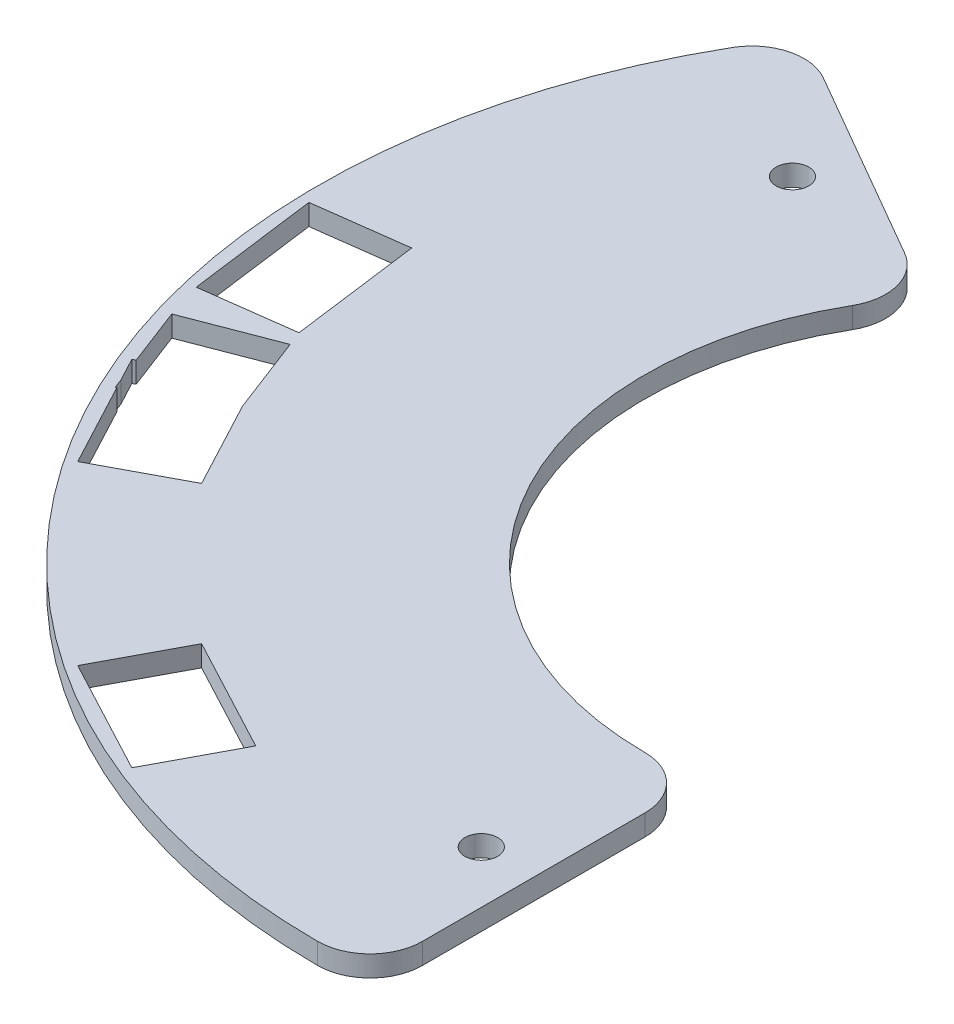
SolidWorks part; units mm, degrees
ref_plane "Front Plane" through (0, 0, 0) normal (0, 0, 1) x (1, 0, 0)
ref_plane "Top Plane" through (0, 0, 0) normal (0, 1, 0) x (1, 0, 0)
ref_plane "Right Plane" through (0, 0, 0) normal (1, 0, 0) x (0, 0, -1)
sketch "Sketch3" plane through (0, 0, 0) normal (0, 1, 0) x (1, 0, 0)
  line L0 (0, -25) -> (0, -50) construction
  line L1 (-21.6506, 12.5) -> (-43.3013, 25) construction
  line L2 (-41.1625, 28.384) -> (-19.3717, 15.8031)
  line L3 (4, -24.6779) -> (4, -49.8397)
  arc A0 (-19.3717, 15.8031) -> (4, -24.6779) centre (0, 0) ccw
  arc A1 (-41.1625, 28.384) -> (4, -49.8397) centre (0, 0) ccw
  circle A2 centre (0, 0) radius 37.5 construction
  circle A3 centre (-32.476, 18.75) radius 1.25
  circle A4 centre (0, -37.5) radius 1.25
  dimension "D1" = 100
  dimension "D2" = 50
  dimension "D6" = 75
  dimension "D7" = 2.5
  dimension "D3" = 120
  dimension "D4" = 4
  dimension "D5" = 4
extrude "Boss-Extrude2" add sketch "Sketch3" along normal mid plane 1.6
sketch "Sketch4" plane through (0, 0, 0) normal (0, 1, 0) x (1, 0, 0)
  line L0 (0, 0) -> (0, -45.5) construction
  line L1 (0, 0) -> (-21.361, -40.1741) construction
  line L2 (0, 0) -> (-40.1741, -21.361) construction
  line L3 (0, 0) -> (-42.4779, -16.3057) construction
  line L4 (0, 0) -> (-45.1107, -5.9389) construction
  line L5 (-24.1325, -34.7364) -> (-15.3031, -39.4312)
  line L6 (-24.1325, -34.7364) -> (-27.4188, -40.9171)
  line L7 (-15.3031, -39.4312) -> (-18.5894, -45.6118)
  line L8 (-27.4188, -40.9171) -> (-18.5894, -45.6118)
  line L9 (-16.9462, -42.5215) -> (-25.7757, -37.8268) construction
  line L10 (-19.7178, -37.0838) -> (-23.0041, -43.2644) construction
  line L11 (-39.4312, -15.3031) -> (-34.7364, -24.1325)
  line L12 (-39.4312, -15.3031) -> (-45.6118, -18.5894)
  line L13 (-34.7364, -24.1325) -> (-40.9171, -27.4188)
  line L14 (-45.6118, -18.5894) -> (-40.9171, -27.4188)
  line L15 (-37.8268, -25.7757) -> (-42.5215, -16.9462) construction
  line L16 (-37.0838, -19.7178) -> (-43.2644, -23.0041) construction
  line L17 (-40.5543, -11.5505) -> (-37.8665, -18.5524)
  line L18 (-40.5543, -11.5505) -> (-47.0893, -14.0591)
  line L19 (-37.8665, -18.5524) -> (-44.4016, -21.061)
  line L20 (-47.0893, -14.0591) -> (-44.4016, -21.061)
  line L21 (-41.134, -19.8067) -> (-43.8218, -12.8048) construction
  line L22 (-39.2104, -15.0515) -> (-45.7454, -17.56) construction
  line L23 (-42.2933, -0.5249) -> (-40.9881, -10.4393)
  line L24 (-42.2933, -0.5249) -> (-49.2334, -1.4386)
  line L25 (-40.9881, -10.4393) -> (-47.9282, -11.353)
  line L26 (-49.2334, -1.4386) -> (-47.9282, -11.353)
  line L27 (-44.4581, -10.8962) -> (-45.7634, -0.9817) construction
  line L28 (-41.6407, -5.4821) -> (-48.5808, -6.3958) construction
  circle A0 centre (0, 0) radius 45.5 construction
  dimension "D5" = 91
  dimension "D1" = 28
  dimension "D2" = 62
  dimension "D3" = 69
  dimension "D4" = 82.5
  dimension "D6" = 10
  dimension "D7" = 7
  dimension "D8" = 7.5
extrude "Cut-Extrude1" cut sketch "Sketch4" against normal through all both and the other way through all contours L23 L25 L26 L24 | L17 L19 L20 L18 | L11 L13 L14 L12 | L5 L7 L8 L6
fillet "Fillet1" radius 4 4 edges at (4, 0, 49.8397) (-41.1625, 0, -28.384) (-19.3717, 0, -15.8031) (4, 0, 24.6779)
equation "\"outer_diameter\"= 100mm"
equation "\"innter_diameter\"= 50mm"
equation "\"mounting_circle_diameter\"= 75mm"
equation "\"D1@Sketch3\"=\"outer_diameter\""
equation "\"D2@Sketch3\"=\"innter_diameter\""
equation "\"D5@Sketch3\"=\"D4@Sketch3\""
equation "\"D6@Sketch3\"=\"mounting_circle_diameter\""
